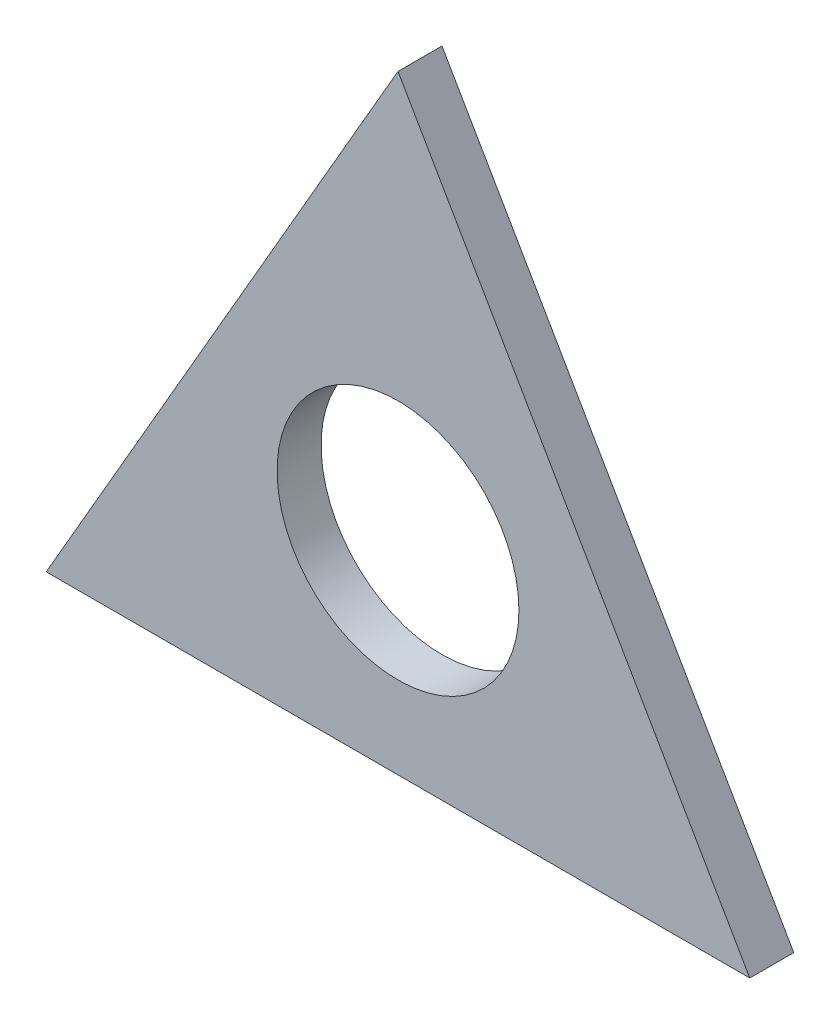
SolidWorks part; units mm, degrees
material "6061-T6 (SS)"
ref_plane "Front Plane" through (0, 0, 0) normal (0, 0, 1) x (1, 0, 0)
ref_plane "Top Plane" through (0, 0, 0) normal (0, 1, 0) x (1, 0, 0)
ref_plane "Right Plane" through (0, 0, 0) normal (1, 0, 0) x (0, 0, -1)
sketch "Sketch1" plane through (0, 0, 0) normal (0, 0, 1) x (1, 0, 0)
  line L0 (0, 0) -> (0, 112.1042) construction
  line L1 (0, 58.6588) -> (-50.8, -29.3294)
  line L2 (-50.8, -29.3294) -> (50.8, -29.3294)
  line L3 (50.8, -29.3294) -> (0, 58.6588)
  circle A0 centre (0, 0) radius 29.3294 construction
  dimension "D1" = 101.6
extrude "Boss-Extrude1" add sketch "Sketch1" along normal blind 6.35
sketch "Sketch2" plane through (0, 0, 6.35) normal (0, 0, 1) x (1, 0, 0)
  circle A0 centre (0, 0) radius 17.4625
  dimension "D1" = 34.925
extrude "Cut-Extrude1" cut sketch "Sketch2" against normal through all
